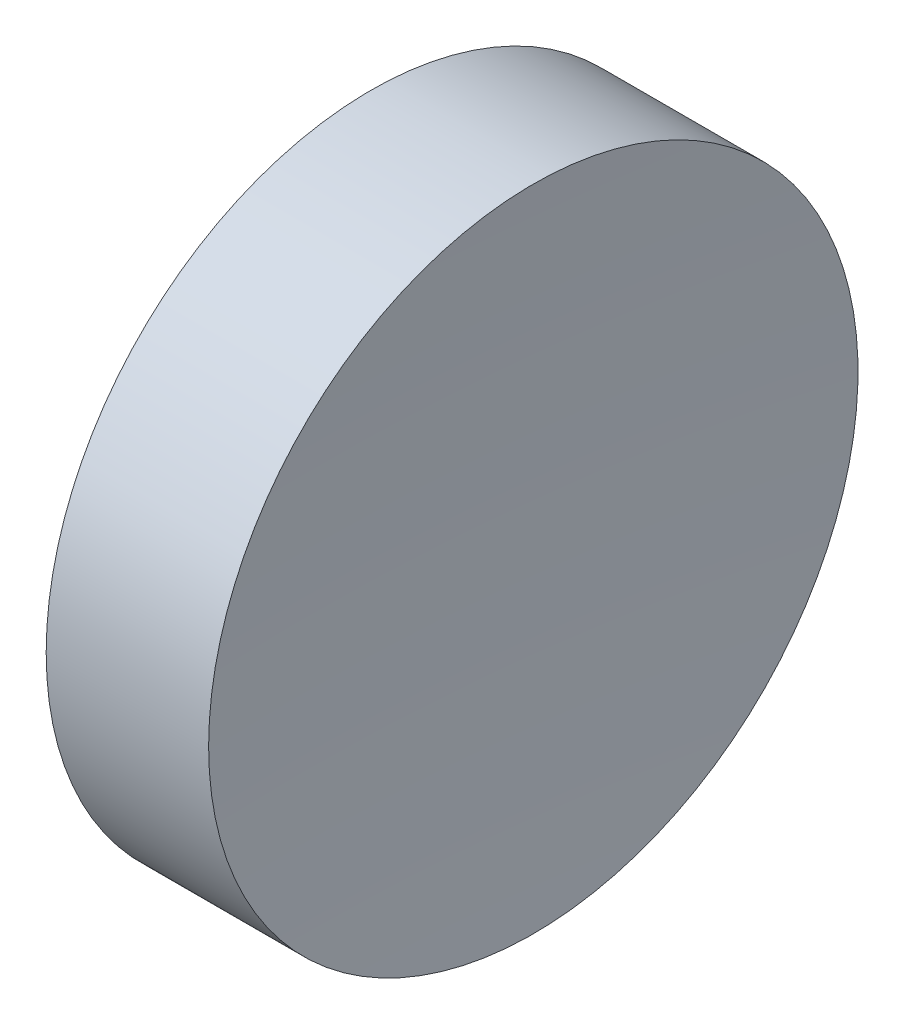
SolidWorks part; units mm, degrees
ref_plane "前视基准面" through (0, 0, 0) normal (0, 0, 1) x (1, 0, 0)
ref_plane "上视基准面" through (0, 0, 0) normal (0, 1, 0) x (1, 0, 0)
ref_plane "右视基准面" through (0, 0, 0) normal (1, 0, 0) x (0, 0, -1)
sketch "草图1" plane through (0, 0, 0) normal (0, 1, 0) x (1, 0, 0)
  line L0 (0, 0) -> (6.9328, 0) construction
  line L1 (0, 0) -> (5.95, 0)
  line L2 (0, 0) -> (0, 12.7)
  line L3 (0, 12.7) -> (6.3536, 12.7)
  arc A0 (6.3536, 12.7) -> (5.95, 0) centre (205.95, 0) ccw
  dimension "D3" = 200
  dimension "D1" = 5.95
  dimension "D2" = 12.7
revolve "旋转1" add sketch "草图1" angle 360 about L0
